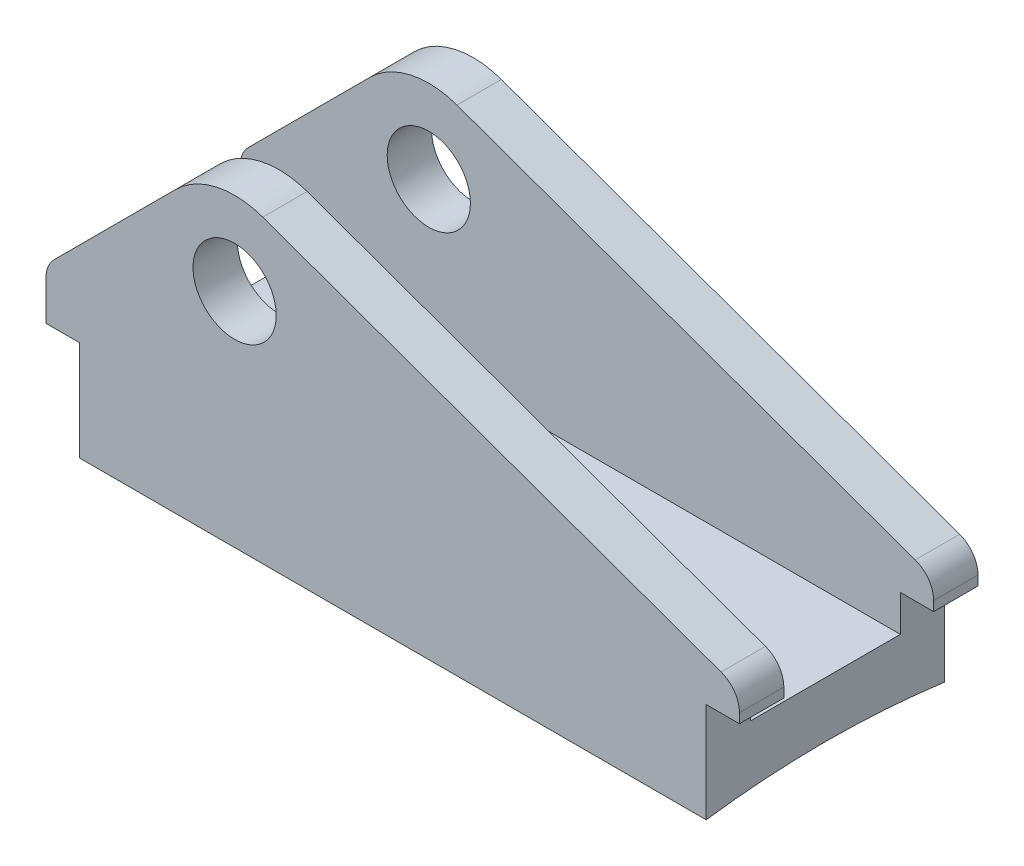
SolidWorks part; units mm, degrees
ref_plane "Front Plane" through (0, 0, 0) normal (0, 0, 1) x (1, 0, 0)
ref_plane "Top Plane" through (0, 0, 0) normal (0, 1, 0) x (1, 0, 0)
ref_plane "Right Plane" through (0, 0, 0) normal (1, 0, 0) x (0, 0, -1)
sketch "Sketch3" plane through (0, 0, 0) normal (1, 0, 0) x (0, 0, -1)
  line L0 (0, 0) -> (0, 384.7703) construction
  line L1 (-21.5, 158.5489) -> (-21.5, 213.5489)
  line L2 (-21.5, 213.5489) -> (-13.5, 213.5489)
  line L3 (-13.5, 213.5489) -> (-13.5, 170)
  line L4 (-13.5, 170) -> (13.5, 170)
  line L5 (13.5, 170) -> (13.5, 213.5489)
  line L6 (13.5, 213.5489) -> (21.5, 213.5489)
  line L7 (21.5, 213.5489) -> (21.5, 158.5489)
  circle A0 centre (0, 0) radius 160
  point P6 (0, 160)
  dimension "D1" = 320
  dimension "D2" = 55
  dimension "D3" = 10
  dimension "D4" = 43
  dimension "D5" = 27
extrude "Boss-Extrude2" add sketch "Sketch3" along normal mid plane 125 contours A0 L0 L4 L3 L2 L1 | L0 A0 L7 L6 L5 L4
sketch "Sketch4" plane through (0, 0, 21.5) normal (0, 0, 1) x (1, 0, 0)
  line L0 (-62.5, 158.5489) -> (-62.5, 213.5489) construction
  line L1 (62.5, 158.5489) -> (-62.5, 158.5489) construction
  line L2 (-61.0355, 187.2266) -> (-39.1066, 209.1555)
  line L3 (-62.5, 183.691) -> (-62.5, 173.0926)
  line L4 (-62.5, 181.7368) -> (-62.5, 213.5489)
  line L5 (-62.5, 158.5489) -> (-56.5, 158.5489)
  line L6 (-62.5, 158.5489) -> (-62.5, 176.5489)
  line L7 (-62.5, 176.5489) -> (-56.5, 176.5489)
  line L8 (-56.5, 158.5489) -> (-56.5, 176.5489)
  line L9 (-62.5, 213.5489) -> (-28.5, 213.5489)
  line L10 (-62.5, 181.7368) -> (72.2999, 181.7368) construction
  line L11 (62.5, 158.5489) -> (56.5, 158.5489)
  line L12 (62.5, 158.5489) -> (62.5, 176.5489)
  line L13 (62.5, 176.5489) -> (56.5, 176.5489)
  line L14 (56.5, 158.5489) -> (56.5, 176.5489)
  line L15 (62.6158, 181.7368) -> (-23.4261, 212.6647)
  line L16 (62.6158, 181.7368) -> (62.5, 213.5489)
  line L17 (62.5, 213.5489) -> (-28.5, 213.5489)
  circle A0 centre (-28.5, 198.5489) radius 7.5
  arc A1 (-23.4261, 212.6647) -> (-39.1066, 209.1555) centre (-28.5, 198.5489) ccw
  arc A2 (-61.0355, 187.2266) -> (-62.5, 183.691) centre (-57.5, 183.691) ccw
  point P12 (-62.5, 185.7621)
  point P27 (62.6158, 181.7368)
  line M14 (-62.5, 213.5489) -> (-62.5, 158.5489)
  line M15 (-62.5, 158.5489) -> (62.5, 158.5489)
  line M16 (62.5, 158.5489) -> (62.5, 213.5489)
  line M17 (62.5, 213.5489) -> (-62.5, 213.5489)
  dimension "D1" = 15
  dimension "D4" = 30
  dimension "D6" = 5
  dimension "D2" = 34
  dimension "D3" = 40
  dimension "D5" = 135
  dimension "D7" = 18
  dimension "D8" = 6
  dimension "D9" = 6
  dimension "D10" = 18
  dimension "D11" = 23.1879
extrude "Cut-Extrude1" cut sketch "Sketch4" against normal blind 125 contours A1 L15 M16 M17 | A2 L2 A1 M17 M14 | L8 L7 M15 M14 | A0 | L14 L13 L12 L11
fillet "Fillet1" radius 5 2 edges at (62.5, 181.7785, -17.5) (62.5, 181.7785, 17.5)
